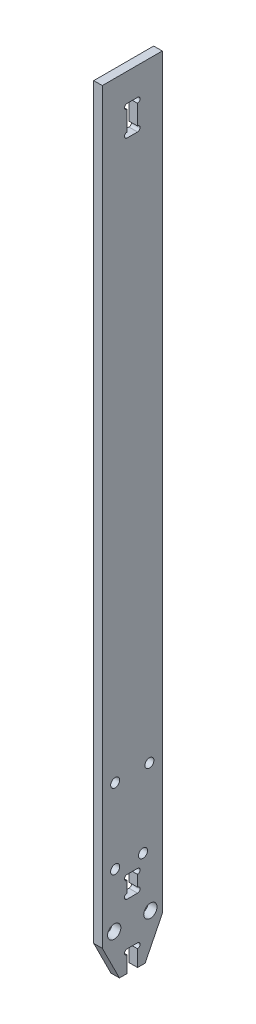
SolidWorks part; units mm, degrees
ref_plane "前视基准面" through (0, 0, 0) normal (0, 0, 1) x (1, 0, 0)
ref_plane "上视基准面" through (0, 0, 0) normal (0, 1, 0) x (1, 0, 0)
ref_plane "右视基准面" through (0, 0, 0) normal (1, 0, 0) x (0, 0, -1)
sketch "草图1" plane through (0, 0, 0) normal (1, 0, 0) x (0, 0, -1)
  line L5 (7, -91.25) -> (-7, -91.25)
  line L6 (7, -91.25) -> (7, 91.25)
  line L7 (7, 91.25) -> (-7, 91.25)
  line L8 (-7, -91.25) -> (-7, 91.25)
  line L9 (7, -91.25) -> (-7, 91.25) construction
  line L10 (7, 91.25) -> (-7, -91.25) construction
  point P0 (0, 0)
  dimension "D1" = 182.5
  dimension "D2" = 14
extrude "凸台-拉伸1" add sketch "草图1" along normal mid plane 2
sketch "草图2" plane through (1, 0, 0) normal (1, 0, 0) x (0, 0, -1)
  line L0 (-7, -91.25) -> (7, -91.25) construction
  line L1 (-1.225, -91.25) -> (1.225, -91.25)
  line L2 (-1.225, -91.25) -> (-1.225, -86.25)
  line L3 (-1.225, -86.25) -> (1.225, -86.25)
  line L4 (1.225, -91.25) -> (1.225, -86.25)
  point P6 (0, -86.25)
  dimension "D1" = 2.45
  dimension "D2" = 5
extrude "切除-拉伸1" cut sketch "草图2" against normal through all
sketch "草图3" plane through (1, 0, 0) normal (1, 0, 0) x (0, 0, -1)
  line L0 (-1.225, -86.25) -> (-1.225, -91.25) construction
  line L1 (1.225, -91.25) -> (1.225, -86.25) construction
  circle A0 centre (-1.225, -86.85) radius 0.6
  circle A1 centre (1.225, -86.85) radius 0.6
  dimension "D1" = 1.2
extrude "切除-拉伸2" cut sketch "草图3" against normal through all
sketch "草图6" plane through (1, 0, 0) normal (1, 0, 0) x (0, 0, -1)
  line L0 (-1.225, -76.2) -> (-1.225, -71.2)
  line L1 (-1.225, -71.2) -> (1.225, -71.2)
  line L2 (1.225, -71.2) -> (1.225, -76.2)
  line L3 (1.225, -76.2) -> (-1.225, -76.2)
  line L4 (-1.225, -87.45) -> (-1.225, -91.25) construction
  line L5 (1.225, -91.25) -> (1.225, -87.45) construction
  line L6 (1.225, -86.25) -> (-1.225, -86.25) construction
  dimension "D1" = 5
  dimension "D2" = 10.05
extrude "切除-拉伸4" cut sketch "草图6" against normal through all
sketch "草图7" plane through (1, 0, 0) normal (1, 0, 0) x (0, 0, -1)
  line L0 (-1.225, -71.2) -> (-1.225, -76.2) construction
  line L1 (1.225, -76.2) -> (1.225, -71.2) construction
  circle A0 centre (-1.225, -71.8) radius 0.6
  circle A1 centre (-1.225, -75.6) radius 0.6
  circle A2 centre (1.225, -71.8) radius 0.6
  circle A3 centre (1.225, -75.6) radius 0.6
  arc A4 (-1.225, -86.25) -> (-1.225, -87.45) centre (-1.225, -86.85) ccw construction
extrude "切除-拉伸5" cut sketch "草图7" against normal through all
sketch "草图8" plane through (1, 0, 0) normal (1, 0, 0) x (0, 0, -1)
  line L0 (-1.225, -72.4) -> (-1.225, -75) construction
  line L1 (-7, -91.25) -> (-1.225, -91.25) construction
  line L2 (0, -76.2) -> (0, -86.25) construction
  line L3 (-1.225, -76.2) -> (1.225, -76.2) construction
  line L4 (1.225, -86.25) -> (-1.225, -86.25) construction
  circle A0 centre (-4.225, -81.25) radius 3 construction
  circle A1 centre (-4.225, -81.25) radius 1.55
  circle A2 centre (4.225, -81.25) radius 1.55
  dimension "D1" = 6
  dimension "D3" = 3.1
  dimension "D2" = 10
extrude "切除-拉伸6" cut sketch "草图8" against normal through all
sketch "草图9" plane through (1, 0, 0) normal (1, 0, 0) x (0, 0, -1)
  line L0 (7, 91.25) -> (-7, 91.25) construction
  line L1 (1.225, 77.75) -> (-1.225, 77.75)
  line L2 (1.225, 77.75) -> (1.225, 84.75)
  line L3 (1.225, 84.75) -> (-1.225, 84.75)
  line L4 (-1.225, 77.75) -> (-1.225, 84.75)
  line L5 (1.225, 77.75) -> (-1.225, 84.75) construction
  line L6 (1.225, 84.75) -> (-1.225, 77.75) construction
  point P0 (0, 81.25)
  dimension "D1" = 10
  dimension "D2" = 7
  dimension "D3" = 2.45
extrude "切除-拉伸7" cut sketch "草图9" against normal through all
sketch "草图10" plane through (1, 0, 0) normal (1, 0, 0) x (0, 0, -1)
  line L0 (-1.225, 84.75) -> (-1.225, 77.75) construction
  line L1 (1.225, 77.75) -> (1.225, 84.75) construction
  circle A0 centre (-1.225, 84.15) radius 0.6
  circle A1 centre (-1.225, 78.35) radius 0.6
  circle A2 centre (1.225, 84.15) radius 0.6
  circle A3 centre (1.225, 78.35) radius 0.6
  dimension "D1" = 1.2
extrude "切除-拉伸8" cut sketch "草图10" against normal through all
sketch "草图11" plane through (1, 0, 0) normal (1, 0, 0) x (0, 0, -1)
  line L0 (0, -86.25) -> (0, -91.25) construction
  line L1 (1.225, -86.25) -> (-1.225, -86.25) construction
  line L2 (-7, -91.25) -> (-1.225, -91.25) construction
  line L3 (-3, -91.25) -> (-7, -83.25)
  line L4 (-7, 91.25) -> (-7, -91.25) construction
  line L5 (-7, -83.25) -> (-7, -91.25)
  line L6 (-7, -91.25) -> (-3, -91.25)
  line L7 (7, -83.25) -> (7, -91.25)
  line L8 (3, -91.25) -> (7, -83.25)
  line L9 (7, -91.25) -> (3, -91.25)
  dimension "D1" = 4
  dimension "D2" = 8
extrude "切除-拉伸9" cut sketch "草图11" against normal through all
sketch "草图12" plane through (1, 0, 0) normal (1, 0, 0) x (0, 0, -1)
  line L0 (-7, -56.75) -> (7, -56.75) construction
  line L1 (-7, 91.25) -> (-7, -83.25) construction
  line L2 (7, -83.25) -> (7, 91.25) construction
  line L3 (1.225, -91.25) -> (3, -91.25) construction
  line L4 (-7, 91.25) -> (-7, -83.25) construction
  circle A0 centre (-4, -68.75) radius 1.05
  dimension "D2" = 12
  dimension "D3" = 3
  dimension "D4" = 2.1
  dimension "D1" = 34.5
extrude "切除-拉伸10" cut sketch "草图12" against normal through all
sketch "草图14" plane through (-1, 0, 0) normal (-1, 0, 0) x (0, 0, 1)
  line L3 (-7, -83.25) -> (-7, 91.25) construction
  line L4 (4, -68.75) -> (-2.5, -68.75) construction
  circle A0 centre (-2.5, -68.75) radius 1.75 construction
  circle A2 centre (-2.5, -68.75) radius 1.05
  circle A3 centre (4, -68.75) radius 1.05 construction
  point P7 (0, 0)
  dimension "D1" = 3.5
  dimension "D2" = 4.5
  dimension "D4" = 2.1
extrude "切除-拉伸11" cut sketch "草图14" against normal through all
sketch "草图15" plane through (-1, 0, 0) normal (-1, 0, 0) x (0, 0, 1)
  line L0 (-4, -51.25) -> (4, -51.25) construction
  circle A0 centre (-4, -51.25) radius 1.05
  circle A1 centre (4, -51.25) radius 1.05
  circle A2 centre (4, -68.75) radius 1.05 construction
  point P6 (0, -51.25)
  dimension "D2" = 17.5
  dimension "D1" = 8
extrude "切除-拉伸12" cut sketch "草图15" against normal through all
